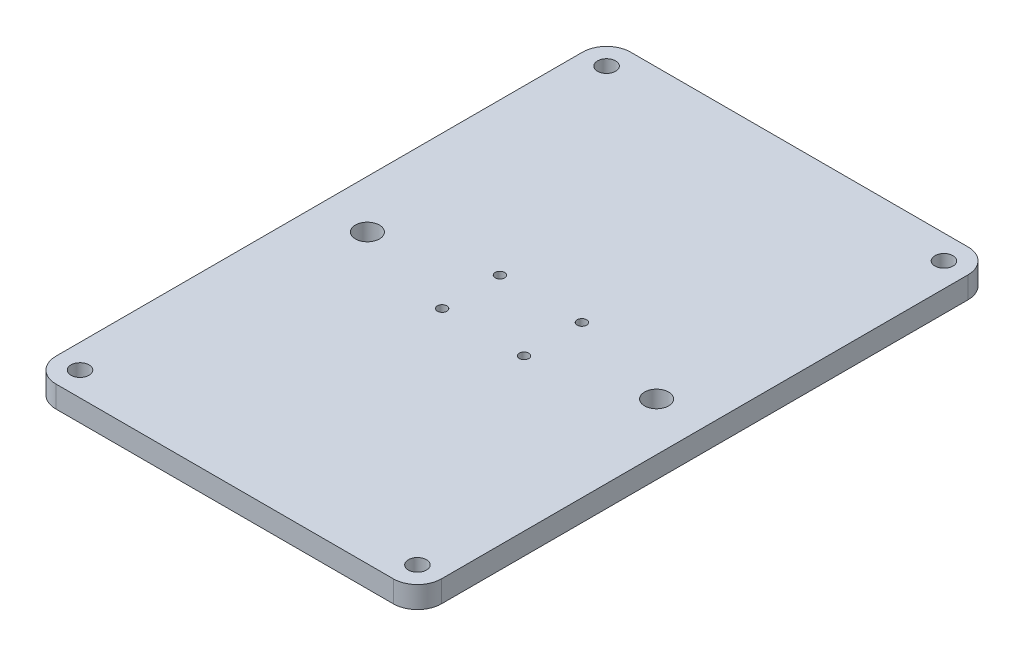
SolidWorks part; units mm, degrees
ref_plane "Front Plane" through (0, 0, 0) normal (0, 0, 1) x (1, 0, 0)
ref_plane "Top Plane" through (0, 0, 0) normal (0, 1, 0) x (1, 0, 0)
ref_plane "Right Plane" through (0, 0, 0) normal (1, 0, 0) x (0, 0, -1)
sketch "Sketch1" plane through (0, -17.55, 0) normal (0, 1, 0) x (1, 0, 0)
  line L1 (-44.45, -75.7199) -> (44.45, -75.7199)
  line L2 (-50.8, -69.3699) -> (-50.8, 69.3699)
  line L3 (-44.45, 75.7199) -> (44.45, 75.7199)
  line L4 (50.8, -69.3699) -> (50.8, 69.3699)
  line L5 (-50.8, -75.7199) -> (50.8, 75.7199) construction
  line L6 (-50.8, 75.7199) -> (50.8, -75.7199) construction
  line L7 (-12.5, -75.7199) -> (0, -75.7199) construction
  line L8 (-38.1, 0) -> (38.1, 0) construction
  line L10 (-44.45, -69.3699) -> (44.45, -69.3699) construction
  line L11 (-44.45, -69.3699) -> (-44.45, 69.3699) construction
  line L12 (-44.45, 69.3699) -> (44.45, 69.3699) construction
  line L13 (44.45, -69.3699) -> (44.45, 69.3699) construction
  line L14 (-44.45, -69.3699) -> (44.45, 69.3699) construction
  line L15 (-44.45, 69.3699) -> (44.45, -69.3699) construction
  arc A0 (44.45, -75.7199) -> (50.8, -69.3699) centre (44.45, -69.3699) ccw
  arc A1 (-44.45, -75.7199) -> (-50.8, -69.3699) centre (-44.45, -69.3699) cw
  arc A2 (-50.8, 69.3699) -> (-44.45, 75.7199) centre (-44.45, 69.3699) cw
  arc A3 (44.45, 75.7199) -> (50.8, 69.3699) centre (44.45, 69.3699) cw
  circle A4 centre (-10.795, 7.62) radius 1.25 construction
  circle A5 centre (-10.795, -7.62) radius 1.25 construction
  circle A6 centre (10.795, -7.62) radius 1.25 construction
  circle A7 centre (10.795, 7.62) radius 1.25 construction
  circle A8 centre (-10.795, 7.62) radius 1.25
  circle A9 centre (-10.795, -7.62) radius 1.25
  circle A10 centre (10.795, -7.62) radius 1.25
  circle A11 centre (10.795, 7.62) radius 1.25
  circle A13 centre (38.1, 0) radius 3.175
  circle A15 centre (-38.1, 0) radius 3.175
  circle A16 centre (44.45, 69.3699) radius 2.3812
  circle A17 centre (-44.45, 69.3699) radius 2.3812
  circle A18 centre (-44.45, -69.3699) radius 2.3812
  circle A19 centre (44.45, -69.3699) radius 2.3812
  point P0 (0, 0)
  point P32 (0, 0)
  dimension "D2" = 6.35
  dimension "D4" = 6.35
  dimension "D5" = 4.7625
  dimension "D1" = 101.6
  dimension "D3" = 6.35
  dimension "D6" = 76.2
extrude "Boss-Extrude1" add sketch "Sketch1" along normal blind 5.715
